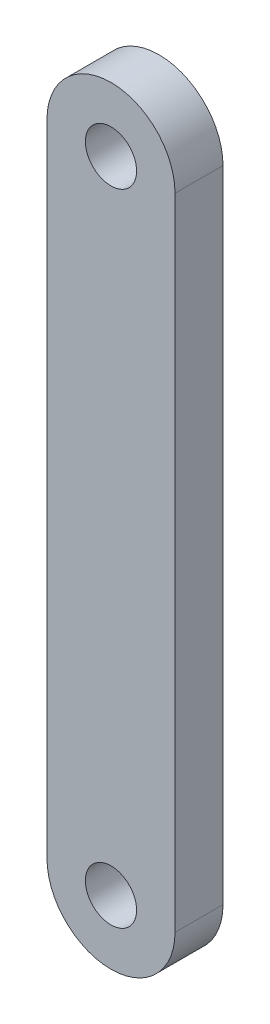
SolidWorks part; units mm, degrees
ref_plane "Front Plane" through (0, 0, 0) normal (0, 0, 1) x (1, 0, 0)
ref_plane "Top Plane" through (0, 0, 0) normal (0, 1, 0) x (1, 0, 0)
ref_plane "Right Plane" through (0, 0, 0) normal (1, 0, 0) x (0, 0, -1)
sketch "Sketch1" plane through (0, 0, 0) normal (0, 0, 1) x (1, 0, 0)
  line L0 (0, 0) -> (0, 40) construction
  line L1 (-4, 0) -> (-4, 40)
  line L2 (4, 0) -> (4, 40)
  arc A0 (-4, 0) -> (4, 0) centre (0, 0) ccw
  arc A1 (4, 40) -> (-4, 40) centre (0, 40) ccw
  point P3 (0, 20)
  dimension "D1" = 40
  dimension "D2" = 8
extrude "Boss-Extrude1" add sketch "Sketch1" against normal blind 3
sketch "Sketch3" plane through (0, 0, 0) normal (0, 0, 1) x (1, 0, 0)
  circle A0 centre (0, 0) radius 1.6
  circle A1 centre (0, 40) radius 1.6
  dimension "D1" = 3.2
  dimension "D2" = 3.2
extrude "Cut-Extrude1" cut sketch "Sketch3" against normal through all
